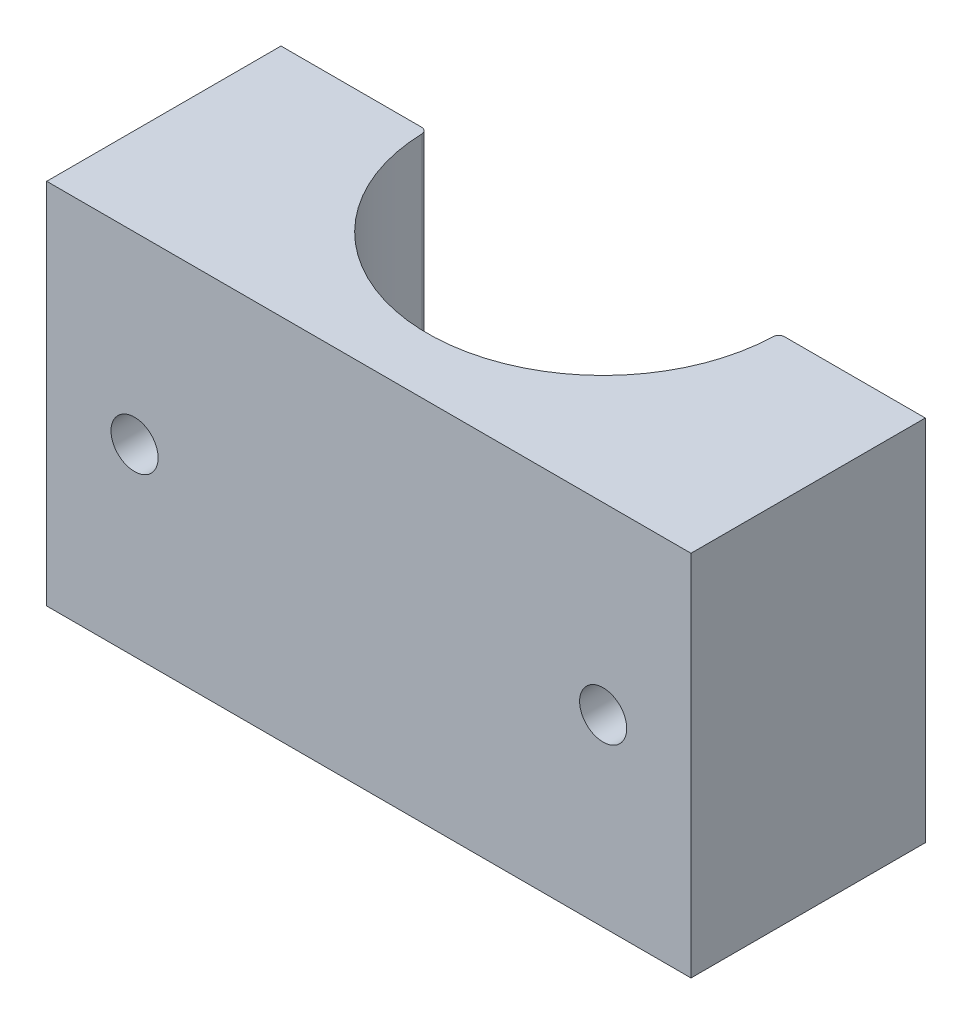
SolidWorks part; units mm, degrees
material "6061-T6 (SS)"
ref_plane "Front Plane" through (0, 0, 0) normal (0, 0, 1) x (1, 0, 0)
ref_plane "Top Plane" through (0, 0, 0) normal (0, 1, 0) x (1, 0, 0)
ref_plane "Right Plane" through (0, 0, 0) normal (1, 0, 0) x (0, 0, -1)
sketch "Sketch5" plane through (0, 0, 0) normal (0, 1, 0) x (1, 0, 0)
  line L0 (-34.925, 0) -> (-19.05, 0) construction
  line L1 (19.05, 0) -> (34.925, 0) construction
  line L2 (-34.925, 0) -> (-34.925, 6.35) construction
  line L3 (-34.925, 6.35) -> (-24.5934, 6.35) construction
  line L4 (34.925, 0) -> (34.925, 6.35) construction
  line L5 (34.925, 6.35) -> (24.5934, 6.35) construction
  line L6 (-34.925, 0) -> (-34.925, -25.4)
  line L7 (-34.925, -25.4) -> (34.925, -25.4)
  line L8 (34.925, -25.4) -> (34.925, 0)
  line L9 (-34.925, 0) -> (-19.05, 0)
  line L10 (19.05, 0) -> (34.925, 0)
  arc A0 (19.05, 0) -> (-19.05, 0) centre (0, 0) ccw construction
  arc A1 (24.5934, 6.35) -> (-24.5934, 6.35) centre (0, 0) ccw construction
  arc A2 (-19.05, 0) -> (19.05, 0) centre (0, 0) ccw
  dimension "D2" = 19.05
  dimension "D4" = 6.35
  dimension "D5" = 25.4
  dimension "D1" = 6.35
  dimension "D3" = 15.875
extrude "Boss-Extrude2" add sketch "Sketch5" against normal blind 39.878
fillet "Fillet1" radius 0.635 2 edges at (19.05, -19.939, 0) (-19.05, -19.939, 0)
hole_wizard "CSK for #10 Flat Head Machine Screw (100)1" positions "Sketch6" profile "Sketch7" countersink size "#10" standard "ANSI Inch" end condition through all
sketch "Sketch6" plane through (0, 0, 0) normal (0, 0, -1) x (-1, 0, 0)
  line L0 (-25.4, -19.939) -> (0, -19.939) construction
  line L2 (-25.4, -19.939) -> (-34.925, -19.939) construction
  line L3 (-34.925, -39.878) -> (-34.925, 0) construction
  point P0 (-25.4, -19.939)
  dimension "D1" = 25.4
sketch "Sketch7" plane through (25.4, -19.939, 0) normal (1, 0, 0) x (0, 1, 0)
  line L0 (0, 0) -> (0, 25.4)
  line L1 (0, 25.4) -> (2.5527, 25.4)
  line L2 (2.5527, 25.4) -> (2.5527, 2.6882)
  line L3 (2.5527, 2.6882) -> (4.8895, 0)
  line L5 (4.8895, 0) -> (0, 0)
  line L6 (-2.5527, 2.6882) -> (-4.8895, 0) construction
  line L11 (0, -6.35) -> (0, 107.95) construction
  dimension "Thru Hole Dia." = 5.1054
  dimension "Thru Hole Depth" = 25.4
  dimension "Near C'Sink Dia." = 9.779
  dimension "Near C'Sink Angle" = 82
hole_wizard "#10 (0.1935) Diameter Hole2" positions "Sketch11" profile "Sketch12" hole size "#10" standard "ANSI Inch"
sketch "Sketch11" plane through (0, 0, 0) normal (0, 0, -1) x (-1, 0, 0)
  line L0 (-30.1625, -7.239) -> (-30.1625, -32.639) construction
  line L4 (-30.1625, -19.939) -> (-34.925, -19.939) construction
  line L5 (-34.925, -39.878) -> (-34.925, 0) construction
  point P0 (-30.1625, -7.239)
  point P2 (-30.1625, -32.639)
  dimension "D1" = 25.4
  dimension "D2" = 4.7625
sketch "Sketch12" plane through (30.1625, -7.239, 0) normal (1, 0, 0) x (0, 1, 0)
  line L0 (0, 0) -> (0, 14.1766)
  line L1 (0, 14.1766) -> (2.4574, 12.7)
  line L2 (2.4574, 12.7) -> (2.4574, 0)
  line L5 (2.4574, 0) -> (0, 0)
  line L10 (0, 14.1766) -> (-2.4575, 12.7) construction
  line L11 (0, -6.35) -> (0, 107.95) construction
  dimension "Hole Dia." = 4.9149
  dimension "Hole Depth" = 12.7
  dimension "Drill Angle" = 118
mirror "Mirror1" about plane through (0, 0, 0) normal (1, 0, 0) of "#10 (0.1935) Diameter Hole2", "CSK for #10 Flat Head Machine Screw (100)1"
